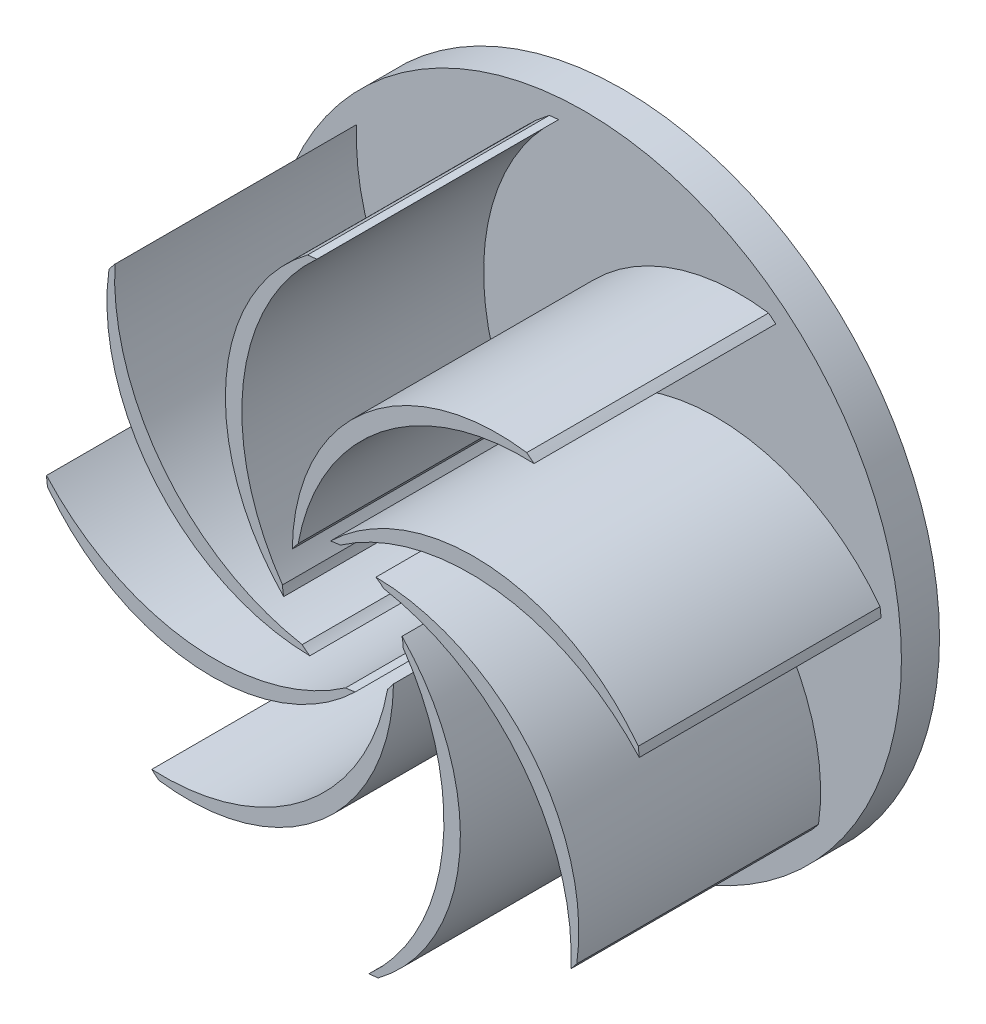
SolidWorks part; units mm, degrees
ref_plane "Front Plane" through (0, 0, 0) normal (0, 0, 1) x (1, 0, 0)
ref_plane "Top Plane" through (0, 0, 0) normal (0, 1, 0) x (1, 0, 0)
ref_plane "Right Plane" through (0, 0, 0) normal (1, 0, 0) x (0, 0, -1)
sketch "Sketch1" plane through (0, 0, 0) normal (0, 0, 1) x (1, 0, 0)
  circle A0 centre (0, 0) radius 33.274
  dimension "D1" = 66.548
extrude "Boss-Extrude1" add sketch "Sketch1" along normal blind 4
sketch "Sketch2" plane through (0, 0, 4) normal (0, 0, 1) x (1, 0, 0)
  circle A0 centre (0, 0) radius 3.048
  dimension "D1" = 6.096
extrude "Cut-Extrude1" cut sketch "Sketch2" against normal through all
sketch "Sketch3" plane through (0, 0, 4) normal (0, 0, 1) x (1, 0, 0)
  line L0 (0, 0) -> (0, 33.274) construction
  line L1 (0, 33.274) -> (0, -33.274) construction
  line L2 (0, -33.274) -> (0, 0) construction
  line L3 (0, 0) -> (33.274, 0) construction
  line L4 (33.274, 0) -> (-33.274, 0) construction
  line L5 (-33.274, 0) -> (0, 0) construction
  line L6 (0, 0) -> (23.5283, 23.5283) construction
  line L7 (0, 0) -> (-23.5283, -23.5283) construction
  line L8 (0, 0) -> (23.5283, -23.5283) construction
  line L9 (0, 0) -> (-23.5283, 23.5283) construction
  line L10 (-23.5283, -23.5283) -> (-3.2584, -3.2584) construction
  circle A0 centre (0, 0) radius 5.08
  circle A1 centre (0, 0) radius 33.274
  arc A4 (0, 5.08) -> (23.5283, -23.5283) centre (0, -18.8993) cw
  arc A5 (5.08, 0) -> (-23.5283, -23.5283) centre (-18.8993, 0) cw
  arc A6 (-5.08, 0) -> (23.5283, 23.5283) centre (18.8993, 0) cw
  arc A7 (0, -5.08) -> (-23.5283, 23.5283) centre (0, 18.8993) cw
  arc A8 (-3.5921, -3.5921) -> (0, 33.274) centre (13.3638, 13.3638) cw
  arc A9 (-3.5921, 3.5921) -> (33.274, 0) centre (13.3638, -13.3638) cw
  arc A10 (3.5921, 3.5921) -> (0, -33.274) centre (-13.3638, -13.3638) cw
  arc A11 (3.5921, -3.5921) -> (-33.274, 0) centre (-13.3638, 13.3638) cw
  arc A12 (-33.274, 0) -> (3.5921, -3.5921) centre (-13.7649, 9.2478) ccw
  arc A13 (0, -5.08) -> (-23.5283, 23.5283) centre (-3.194, 16.2724) cw
  arc A14 (-3.5921, -3.5921) -> (0, 33.274) centre (9.2478, 13.7649) cw
  arc A15 (-5.08, 0) -> (23.5283, 23.5283) centre (16.2724, 3.194) cw
  arc A16 (-3.5921, 3.5921) -> (33.274, 0) centre (13.7649, -9.2478) cw
  arc A17 (0, 5.08) -> (23.5283, -23.5283) centre (3.194, -16.2724) cw
  arc A18 (3.5921, 3.5921) -> (0, -33.274) centre (-9.2478, -13.7649) cw
  arc A19 (5.08, 0) -> (-23.5283, -23.5283) centre (-16.2724, -3.194) cw
  point P37 (-15.8586, -12.2404)
  dimension "D1" = 10.16
  dimension "D7" = 66.548
  dimension "D2" = 45
  dimension "D3" = 45
  dimension "D4" = 45
  dimension "D5" = 45
extrude "Boss-Extrude2" add sketch "Sketch3" along normal blind 25.4 contours A19 A5 | A11 A12 | A13 A7 | A14 A8 | A15 A6 | A16 A9 | A17 A4 | A18 A10
sketch "Sketch4" plane through (0, 0, 4) normal (0, 0, 1) x (1, 0, 0)
  circle A0 centre (0, 0) radius 6.35
  dimension "D1" = 12.7
extrude "Cut-Extrude2" cut sketch "Sketch4" along normal blind 56.896
sketch "Sketch5" plane through (0, 0, 4) normal (0, 0, 1) x (1, 0, 0)
  circle A0 centre (0, 0) radius 33.274
  circle A1 centre (0, 0) radius 31.2532
  dimension "D1" = 2.0208
extrude "Cut-Extrude3" cut sketch "Sketch5" along normal blind 120.142
